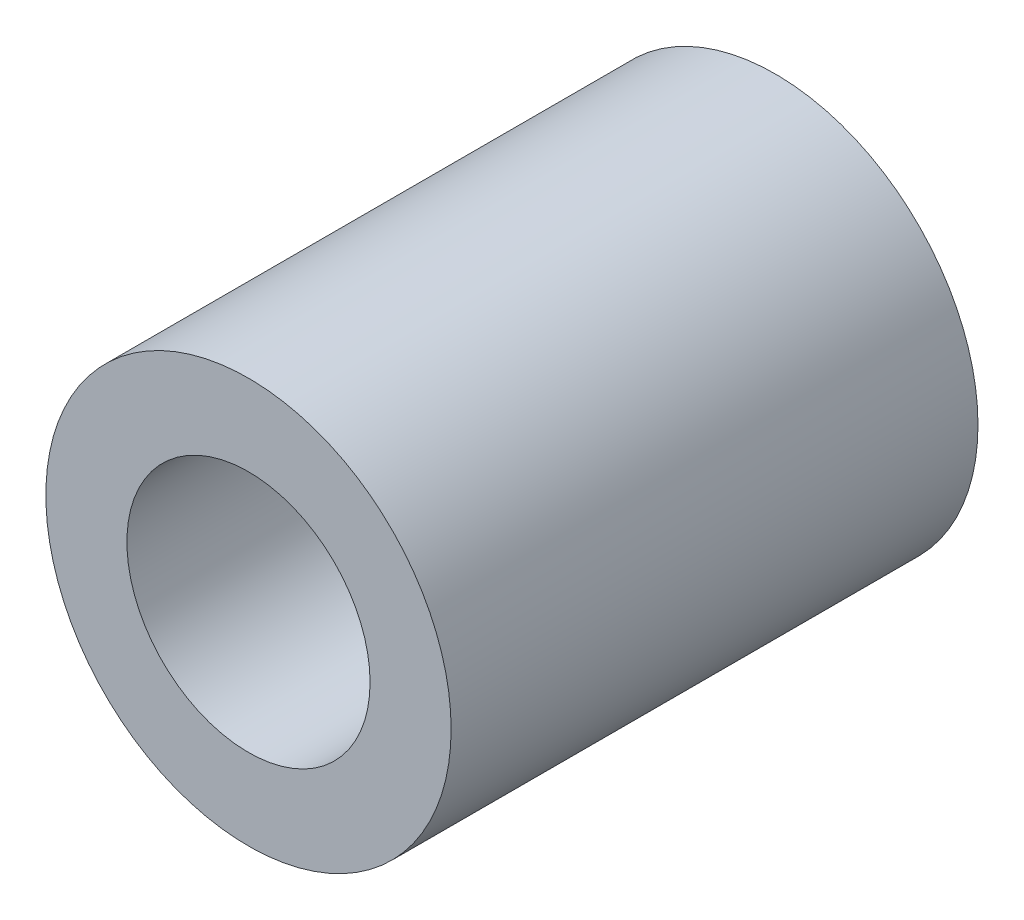
SolidWorks part; units mm, degrees
ref_plane "Plan de face" through (0, 0, 0) normal (0, 0, 1) x (1, 0, 0)
ref_plane "Plan de dessus" through (0, 0, 0) normal (0, 1, 0) x (1, 0, 0)
ref_plane "Plan de droite" through (0, 0, 0) normal (1, 0, 0) x (0, 0, -1)
sketch "Esquisse1" plane through (0, 0, 0) normal (0, 0, 1) x (1, 0, 0)
  circle A0 centre (0, 0) radius 3
  circle A1 centre (0, 0) radius 5
  dimension "D1" = 6
  dimension "D2" = 10
extrude "Boss.-Extru.1" add sketch "Esquisse1" along normal blind 13
